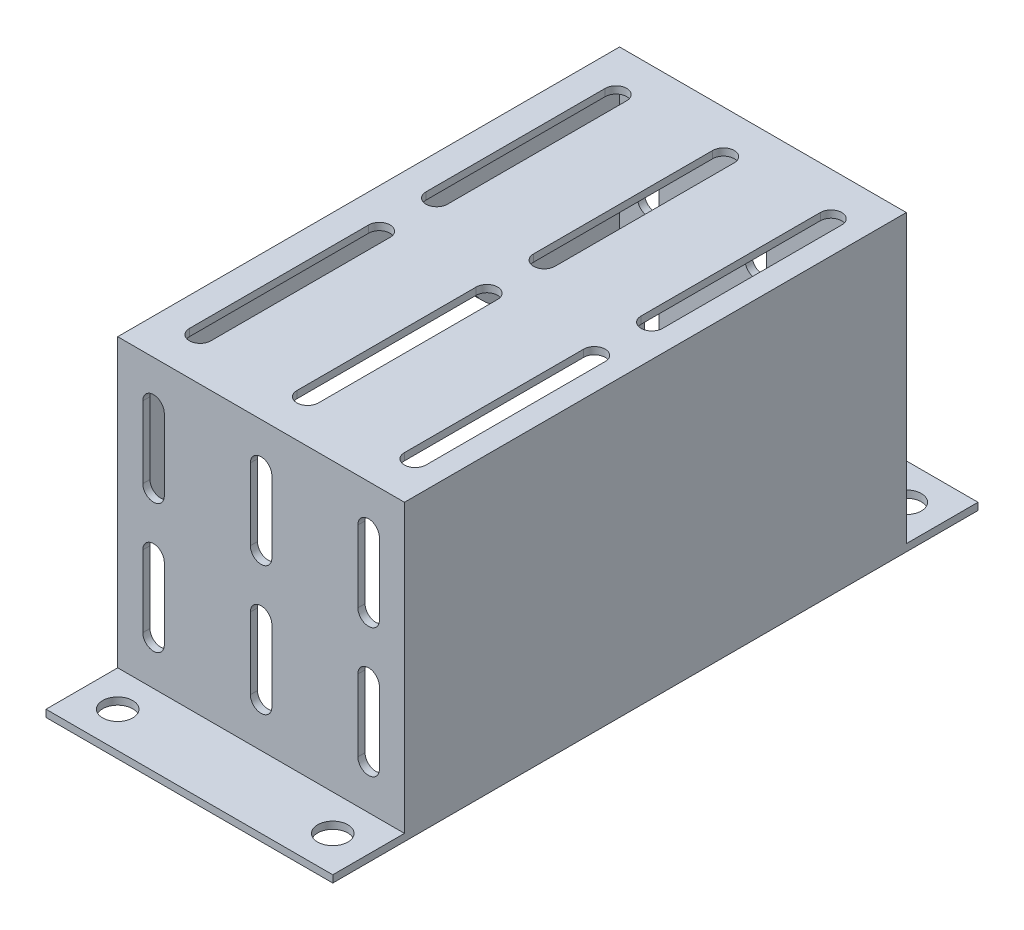
SolidWorks part; units mm, degrees
material "冷轧钢板"
ref_plane "前视基准面" through (0, 0, 0) normal (0, 0, 1) x (1, 0, 0)
ref_plane "上视基准面" through (0, 0, 0) normal (0, 1, 0) x (1, 0, 0)
ref_plane "右视基准面" through (0, 0, 0) normal (1, 0, 0) x (0, 0, -1)
sketch "草图1" plane through (0, 0, 0) normal (1, 0, 0) x (0, 0, -1)
  line L0 (0, 0) -> (10, 0)
  line L1 (10, 0) -> (10, 40)
  line L2 (10, 40) -> (80, 40)
  line L3 (80, 40) -> (80, 0)
  line L4 (80, 0) -> (90, 0)
  line L5 (0, -1) -> (11, -1)
  line L6 (11, -1) -> (11, 39)
  line L7 (11, 39) -> (79, 39)
  line L8 (79, 39) -> (79, -1)
  line L9 (79, -1) -> (90, -1)
  line L10 (0, 0) -> (0, -1)
  line L11 (90, 0) -> (90, -1)
  dimension "D1" = 10
  dimension "D2" = 10
  dimension "D3" = 70
  dimension "D4" = 40
  dimension "D5" = 1
extrude "凸台-拉伸1" add sketch "草图1" along normal blind 40
sketch "草图2" plane through (40, 0, 0) normal (1, 0, 0) x (0, 0, -1)
  line L0 (79, -1) -> (90, -1) construction
  line L1 (10, 40) -> (80, 40)
  line L2 (10, 40) -> (10, -1)
  line L3 (10, -1) -> (80, -1)
  line L4 (80, 40) -> (80, -1)
  line L5 (80, 0) -> (80, 40) construction
  dimension "D1" = 0
extrude "凸台-拉伸2" add sketch "草图2" against normal blind 1
sketch "草图3" plane through (0, 0, 0) normal (-1, 0, 0) x (0, 0, 1)
  line L0 (0, -1) -> (-11, -1) construction
  line L1 (-80, 40) -> (-10, 40)
  line L2 (-80, 40) -> (-80, -1)
  line L3 (-80, -1) -> (-10, -1)
  line L4 (-10, 40) -> (-10, -1)
  line L5 (-10, 40) -> (-10, 0) construction
  dimension "D1" = 0
extrude "凸台-拉伸3" add sketch "草图3" against normal blind 1
sketch "草图4" plane through (0, 0, 0) normal (0, 1, 0) x (1, 0, 0)
  line L0 (20, 90) -> (20, -2.3334) construction
  line L1 (40, 90) -> (0, 90) construction
  line L2 (0, 45) -> (49.0224, 45) construction
  line L3 (0, 80) -> (0, 10) construction
  circle A0 centre (5, 85) radius 2.1
  circle A1 centre (35, 85) radius 2.1
  circle A2 centre (35, 5) radius 2.1
  circle A3 centre (5, 5) radius 2.1
  dimension "D1" = 30
  dimension "D2" = 80
  dimension "D3" = 80
  dimension "D4" = 4.2
extrude "切除-拉伸1" cut sketch "草图4" against normal blind 1
sketch "草图5" plane through (0, 0, 0) normal (-1, 0, 0) x (0, 0, 1)
  line L0 (-45, 15) -> (-45, -16.5026) construction
  line L1 (-30, 15) -> (-30, -16.5026)
  line L2 (-60, 15) -> (-60, -16.5026)
  line L3 (-10, 40) -> (-10, 0) construction
  line L4 (-80, 40) -> (-10, 40) construction
  arc A0 (-30, 15) -> (-60, 15) centre (-45, 15) ccw
  arc A1 (-60, -16.5026) -> (-30, -16.5026) centre (-45, -16.5026) ccw
  point P2 (-45, -0.7513)
  dimension "D3" = 25
  dimension "D1" = 35
  dimension "D2" = 30
extrude "切除-拉伸2" cut sketch "草图5" against normal blind 1
sketch "草图6" plane through (0, 0, -10) normal (0, 0, 1) x (1, 0, 0)
  line L0 (5, 34) -> (5, 24) construction
  line L1 (6.5, 34) -> (6.5, 24)
  line L2 (3.5, 34) -> (3.5, 24)
  line L3 (5, 16) -> (5, 6) construction
  line L4 (6.5, 16) -> (6.5, 6)
  line L5 (3.5, 16) -> (3.5, 6)
  line L6 (40, 40) -> (0, 40) construction
  line L7 (40, 0) -> (0, 0) construction
  line L8 (0, 40) -> (0, 0) construction
  arc A0 (6.5, 34) -> (3.5, 34) centre (5, 34) ccw
  arc A1 (3.5, 24) -> (6.5, 24) centre (5, 24) ccw
  arc A2 (6.5, 16) -> (3.5, 16) centre (5, 16) ccw
  arc A3 (3.5, 6) -> (6.5, 6) centre (5, 6) ccw
  point P2 (5, 29)
  point P7 (5, 11)
  dimension "D3" = 6
  dimension "D4" = 6
  dimension "D1" = 3
  dimension "D2" = 10
  dimension "D5" = 5
extrude "切除-拉伸3" cut sketch "草图6" against normal through all
pattern_linear "阵列(线性)1" count 3 spacing 15 along (1, 0, 0) of "切除-拉伸3"
sketch "草图7" plane through (0, 40, 0) normal (0, 1, 0) x (1, 0, 0)
  line L0 (5.5, 74) -> (5.5, 49) construction
  line L1 (7, 74) -> (7, 49)
  line L2 (4, 74) -> (4, 49)
  line L3 (5.5, 41) -> (5.5, 16) construction
  line L4 (7, 41) -> (7, 16)
  line L5 (4, 41) -> (4, 16)
  line L6 (40, 80) -> (0, 80) construction
  line L7 (40, 10) -> (0, 10) construction
  line L8 (0, 80) -> (0, 10) construction
  arc A0 (7, 74) -> (4, 74) centre (5.5, 74) ccw
  arc A1 (4, 49) -> (7, 49) centre (5.5, 49) ccw
  arc A2 (7, 41) -> (4, 41) centre (5.5, 41) ccw
  arc A3 (4, 16) -> (7, 16) centre (5.5, 16) ccw
  point P2 (5.5, 61.5)
  point P7 (5.5, 28.5)
  dimension "D4" = 6
  dimension "D1" = 3
  dimension "D2" = 6
  dimension "D3" = 25
  dimension "D5" = 4
extrude "切除-拉伸4" cut sketch "草图7" against normal blind 1
pattern_linear "阵列(线性)2" count 3 spacing 15 along (1, 0, 0) of "切除-拉伸4"
sketch "草图8" plane through (0, 0, 0) normal (-1, 0, 0) x (0, 0, 1)
  line L0 (-60, -1) -> (-90, -1) construction
  line L1 (-79, -1) -> (-11, -1)
  line L2 (-79, -1) -> (-79, 17)
  line L3 (-79, 17) -> (-11, 17)
  line L4 (-11, -1) -> (-11, 17)
  line L5 (-80, 0) -> (-80, 40) construction
  line L6 (-10, 40) -> (-10, 0) construction
  line L7 (0, -1) -> (-30, -1) construction
  dimension "D1" = 1
  dimension "D2" = 1
  dimension "D3" = 18
extrude "切除-拉伸5" cut sketch "草图8" against normal blind 10
fillet "圆角1" radius 10 2 edges at (0.5, 17, -59.8661) (0.5, 17, -30.1339)
